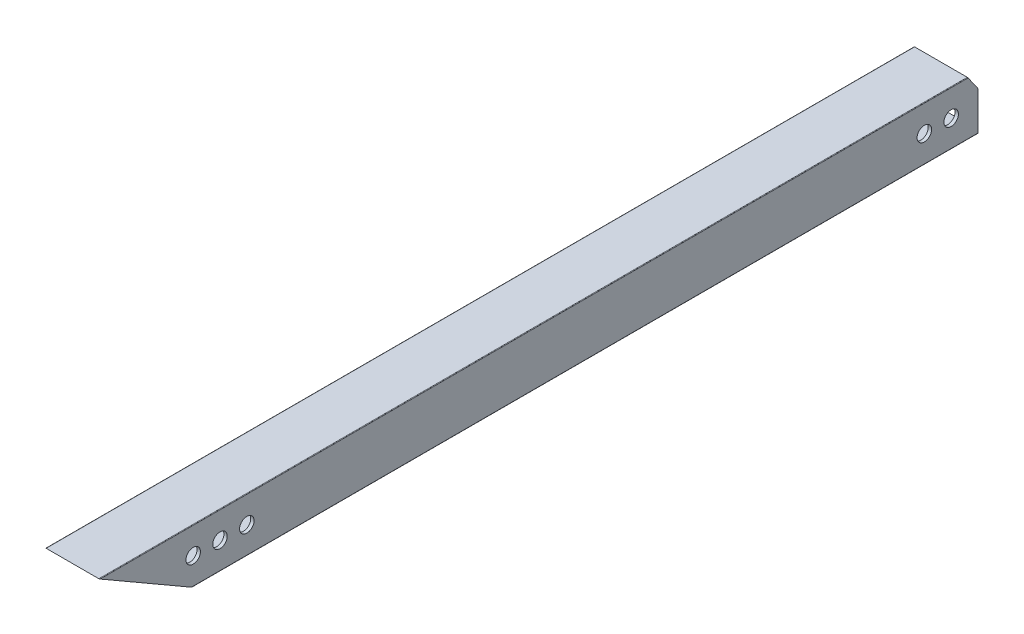
SolidWorks part; units mm, degrees
ref_plane "Front Plane" through (0, 0, 0) normal (0, 0, 1) x (1, 0, 0)
ref_plane "Top Plane" through (0, 0, 0) normal (0, 1, 0) x (1, 0, 0)
ref_plane "Right Plane" through (0, 0, 0) normal (1, 0, 0) x (0, 0, -1)
sketch "Sketch1" plane through (0, 0, 0) normal (0, 0, 1) x (1, 0, 0)
  line L0 (-11.1125, -9.5885) -> (-11.1125, 9.5885)
  line L1 (-12.446, -12.7) -> (12.446, -12.7)
  line L2 (-12.7, -12.446) -> (-12.7, 12.446)
  line L3 (-12.446, 12.7) -> (12.446, 12.7)
  line L4 (12.7, -12.446) -> (12.7, 12.446)
  line L5 (-12.7, -12.7) -> (12.7, 12.7) construction
  line L6 (-12.7, 12.7) -> (12.7, -12.7) construction
  line L7 (-9.5885, 11.1125) -> (9.5885, 11.1125)
  line L8 (11.1125, -9.5885) -> (11.1125, 9.5885)
  line L9 (-9.5885, -11.1125) -> (9.5885, -11.1125)
  line L10 (-12.7, -12.7) -> (12.7, -12.7) construction
  line L11 (-12.7, -12.7) -> (-12.7, 12.7) construction
  line L12 (12.7, -12.7) -> (12.7, 12.7) construction
  line L13 (-12.7, 12.7) -> (12.7, 12.7) construction
  line L14 (-11.1125, -11.1125) -> (-11.1125, 11.1125) construction
  line L15 (-11.1125, -11.1125) -> (11.1125, -11.1125) construction
  line L16 (11.1125, -11.1125) -> (11.1125, 11.1125) construction
  line L17 (-11.1125, 11.1125) -> (11.1125, 11.1125) construction
  arc A0 (-12.446, -12.7) -> (-12.7, -12.446) centre (-12.446, -12.446) cw
  arc A1 (12.446, -12.7) -> (12.7, -12.446) centre (12.446, -12.446) ccw
  arc A2 (12.446, 12.7) -> (12.7, 12.446) centre (12.446, 12.446) cw
  arc A3 (-12.7, 12.446) -> (-12.446, 12.7) centre (-12.446, 12.446) cw
  arc A4 (-11.1125, -9.5885) -> (-9.5885, -11.1125) centre (-9.5885, -9.5885) ccw
  arc A5 (11.1125, -9.5885) -> (9.5885, -11.1125) centre (9.5885, -9.5885) cw
  arc A6 (9.5885, 11.1125) -> (11.1125, 9.5885) centre (9.5885, 9.5885) cw
  arc A7 (-11.1125, 9.5885) -> (-9.5885, 11.1125) centre (-9.5885, 9.5885) cw
  point P0 (0, 0)
  dimension "D4" = 0.254
  dimension "D5" = 1.524
  dimension "D1" = 25.4
  dimension "D2" = 25.4
  dimension "D3" = 1.5875
extrude "Boss-Extrude1" add sketch "Sketch1" along normal blind 415.925
sketch "Sketch2" plane through (-12.7, 0, 0) normal (-1, 0, 0) x (0, 0, 1)
  line L0 (415.925, 12.7) -> (371.9309, -12.7)
  line L1 (415.925, -12.7) -> (0, -12.7) construction
  line L2 (371.9309, -12.7) -> (415.925, -12.7)
  line L3 (415.925, -12.7) -> (415.925, 12.7)
  line L4 (415.925, 12.7) -> (0, 12.7) construction
  line L5 (415.925, 0) -> (0, 0) construction
  line L6 (0, -13.97) -> (0, 13.97) construction
  line L7 (12.7, 0) -> (25.4, 0) construction
  line L8 (0, 5.7807) -> (4.8449, 12.7)
  line L9 (4.8449, 12.7) -> (0, 12.7)
  line L10 (0, 12.7) -> (0, 5.7807)
  circle A0 centre (371.475, 0) radius 3.429
  circle A1 centre (358.775, 0) radius 3.429
  circle A2 centre (346.075, 0) radius 3.429
  circle A3 centre (12.7, 0) radius 3.429
  circle A4 centre (25.4, 0) radius 3.429
  dimension "D2" = 6.858
  dimension "D3" = 44.45
  dimension "D5" = 12.7
  dimension "D6" = 12.7
  dimension "D1" = 30
  dimension "D8" = 12.7
  dimension "D9" = 3.9688
  dimension "D10" = 125
  dimension "D4" = 3
  dimension "D7" = 2
extrude "Cut-Extrude1" cut sketch "Sketch2" against normal through all
